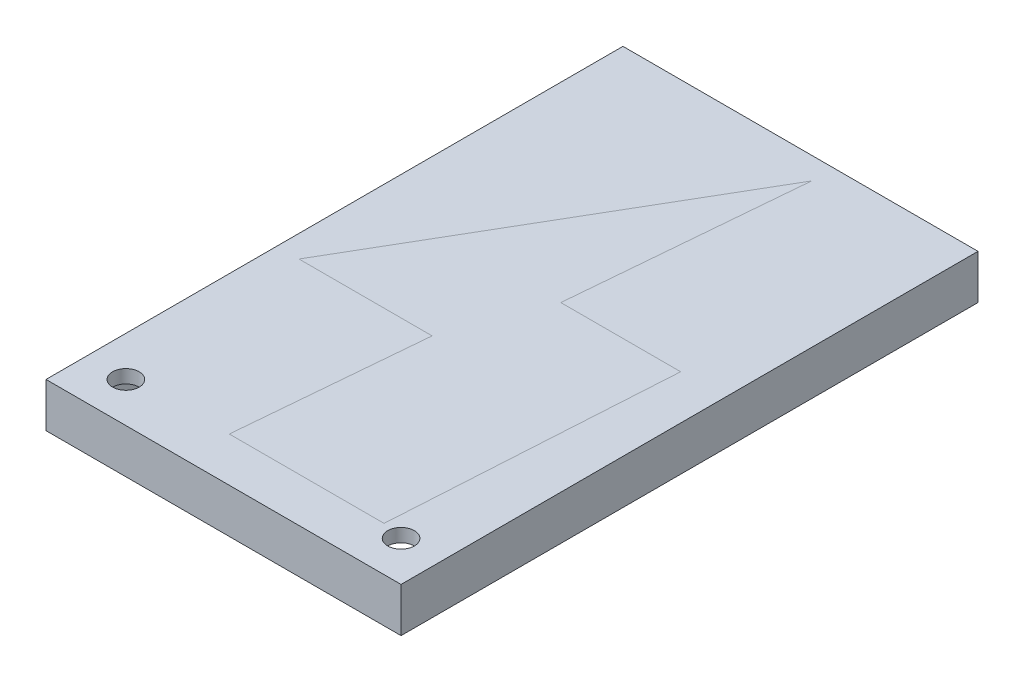
SolidWorks part; units mm, degrees
ref_plane "Płaszczyzna XY" through (0, 0, 0) normal (0, 0, 1) x (1, 0, 0)
ref_plane "Płaszczyzna XZ" through (0, 0, 0) normal (0, 1, 0) x (1, 0, 0)
ref_plane "Płaszczyzna YZ" through (0, 0, 0) normal (1, 0, 0) x (0, 0, -1)
ref_plane "Plane1" through (0, -7, 0) normal (0, -1, 0) x (1, 0, 0)
sketch "Sketch1" plane through (0, -7, 0) normal (0, -1, 0) x (1, 0, 0)
  line L0 (-75, -5) -> (5, -5)
  line L1 (5, -5) -> (5, 125)
  line L2 (5, 125) -> (-75, 125)
  line L3 (-75, 125) -> (-75, -5)
extrude "Boss-Extrude1" add sketch "Sketch1" against normal blind 10
sketch "Sketch2" plane through (0, -7, 0) normal (0, -1, 0) x (1, 0, 0)
  line L0 (-70, 0) -> (0, 0)
  line L1 (0, 0) -> (0, 120)
  line L2 (0, 120) -> (-70, 120)
  line L3 (-70, 120) -> (-70, 0)
extrude "Cut-Extrude1" cut sketch "Sketch2" against normal blind 7
sketch "Sketch3" plane through (0, 3, 0) normal (0, 1, 0) x (-1, 0, 0)
  line L0 (40, 115) -> (8.831, 115)
  line L1 (8.831, 115) -> (8.831, 52)
  line L2 (8.831, 52) -> (32, 52)
  line L3 (32, 52) -> (27.4764, 0)
  line L4 (27.4764, 0) -> (70, 73)
  line L5 (70, 73) -> (40, 73)
  line L6 (40, 73) -> (40, 115)
extrude "Cut-Extrude2" cut sketch "Sketch3" against normal through all
draft "Draft1" type of draft neutral plane draft angle 5.034 faces to draft 1 face at (-40, 1.5, 94) neutral plane through (-70, -7, 73) neutral plane normal (0, 0, -1) reverse direction yes parameters "D1"=5.034
draft "Draft2" type of draft neutral plane draft angle 3.48 faces to draft 1 face at (-8.831, 1.5, 83.5) neutral plane through (-40, -7, 115) neutral plane normal (0, 0, -1) parameters "D1"=3.48
hole_wizard "Ø6.0 (6) Diameter Hole1" positions "Sketch5" profile "Sketch4" hole size "Ø6.0" standard "ANSI Metric"
sketch "Sketch5" plane through (0, 3, 0) normal (0, 1, 0) x (1, 0, 0)
  point P0 (-66, -116)
  point P1 (-4, -116)
sketch "Sketch4" plane through (-66, 3, 116) normal (1, 0, 0) x (0, 0, 1)
  line L0 (0, 0) -> (0, 10)
  line L1 (0, 10) -> (3, 10)
  line L2 (3, 10) -> (3, 0)
  line L5 (3, 0) -> (0, 0)
  line L11 (0, -6.35) -> (0, 107.95) construction
  dimension "Thru Hole Dia." = 6
  dimension "Thru Hole Depth" = 10
ref_plane "Plane2" through (-35, 0, 0) normal (-1, 0, 0) x (0, 0, 1)
sketch "Sketch6" plane through (0, 3, 0) normal (0, 1, 0) x (1, 0, 0)
  line L0 (-5, -52) -> (-32, -52) construction
  line L1 (-32, -52) -> (-27.4764, 0) construction
  line L2 (-27.4764, 0) -> (-70, -73) construction
  line L3 (-70, -73) -> (-40, -73) construction
  line L4 (-40, -73) -> (-43.6995, -115) construction
  line L5 (-43.6995, -115) -> (-8.831, -115) construction
  line L6 (-8.831, -115) -> (-5, -52) construction
  line L7 (-5, -52) -> (-32, -52)
  line L8 (-32, -52) -> (-27.4764, 0)
  line L9 (-27.4764, 0) -> (-70, -73)
  line L10 (-70, -73) -> (-40, -73)
  line L11 (-40, -73) -> (-43.6995, -115)
  line L12 (-43.6995, -115) -> (-8.831, -115)
  line L13 (-8.831, -115) -> (-5, -52)
extrude "Boss-Extrude2" add sketch "Sketch6" against normal blind 1 separate body
